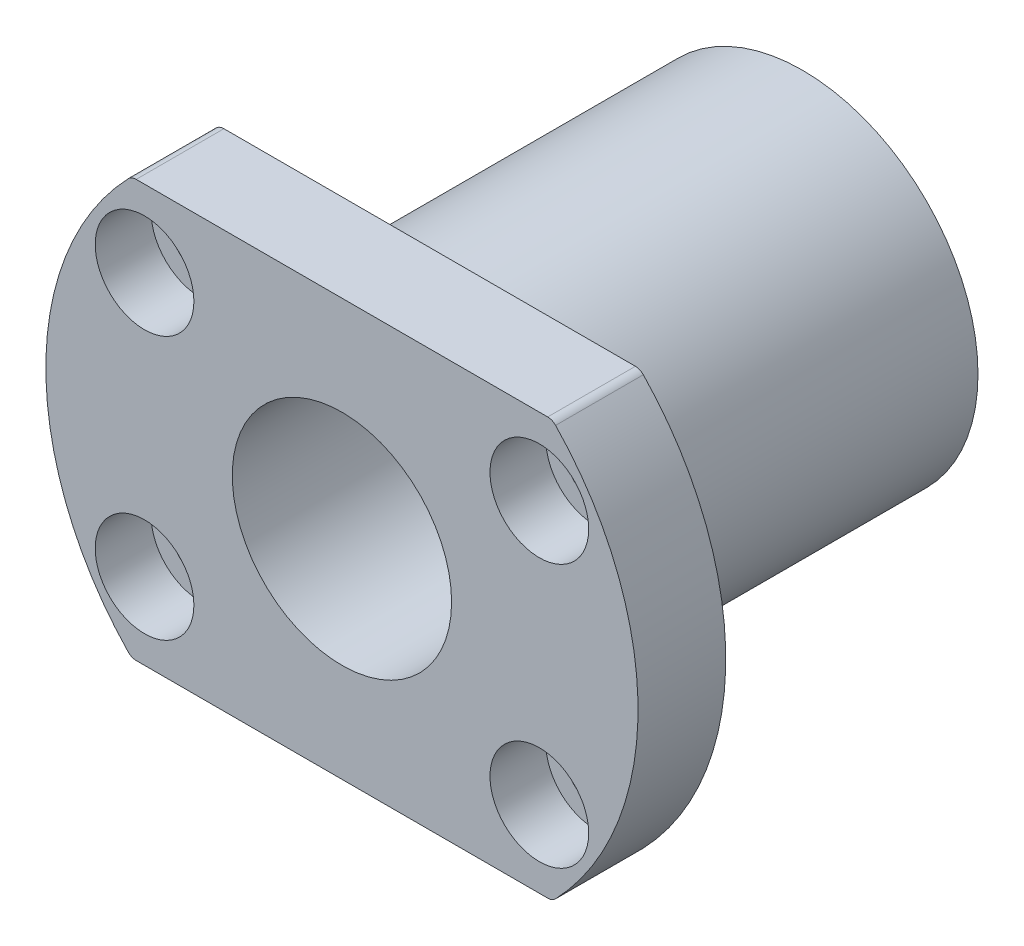
SolidWorks part; units mm, degrees
ref_plane "Front Plane" through (0, 0, 0) normal (0, 0, 1) x (1, 0, 0)
ref_plane "Top Plane" through (0, 0, 0) normal (0, 1, 0) x (1, 0, 0)
ref_plane "Right Plane" through (0, 0, 0) normal (1, 0, 0) x (0, 0, -1)
sketch "Sketch1" plane through (0, 0, 0) normal (0, 0, 1) x (1, 0, 0)
  circle A0 centre (0, 0) radius 16
  circle A1 centre (0, 0) radius 10
  dimension "D1" = 20
  dimension "D2" = 32
extrude "Boss-Extrude1" add sketch "Sketch1" along normal blind 34
sketch "Sketch2" plane through (0, 0, 34) normal (0, 0, 1) x (1, 0, 0)
  line L0 (0, 0) -> (31.8215, 0) construction
  line L1 (-19.1833, -19) -> (19.1833, -19)
  line L2 (-19.1833, 19) -> (19.1833, 19)
  arc A0 (19.1833, -19) -> (19.1833, 19) centre (0, 0) ccw
  arc A1 (-19.1833, 19) -> (-19.1833, -19) centre (0, 0) ccw
  circle A2 centre (0, 0) radius 10 construction
  circle A3 centre (0, 0) radius 10
  dimension "D1" = 54
  dimension "D2" = 19
extrude "Boss-Extrude2" add sketch "Sketch2" along normal blind 8
sketch "Sketch3" plane through (0, 0, 42) normal (0, 0, 1) x (1, 0, 0)
  line L0 (0, 0) -> (0, 22.5899) construction
  line L1 (0, 0) -> (-30.772, 0) construction
  circle A0 centre (-18, 12) radius 3.5851
  circle A1 centre (-18, -12) radius 3.5851
  circle A2 centre (18, 12) radius 3.5851
  circle A3 centre (18, -12) radius 3.5851
  dimension "D1" = 18
  dimension "D2" = 12
hole_wizard "CBORE for M5 Hex Socket Head Cap Screw1" positions "3DSketch1" profile "Sketch4" counterbore size "M5" standard "ISO" end condition through all
sketch3d "3DSketch1"
  point P0 (-18, -12, 42)
  point P3 (-18, 12, 42)
  point P6 (18, 12, 42)
  point P9 (18, -12, 42)
sketch "Sketch4" plane through (-18, -12, 42) normal (1, 0, 0) x (0, -1, 0)
  line L0 (0, 0) -> (0, 42)
  line L1 (0, 42) -> (2.75, 42)
  line L3 (2.75, 42) -> (2.75, 5.1)
  line L4 (2.75, 5.1) -> (4.5, 5.1)
  line L5 (4.5, 5.1) -> (4.5, 0)
  line L7 (4.5, 0) -> (0, 0)
  line L11 (0, -6.35) -> (0, 107.95) construction
  dimension "Thru Hole Dia." = 5.5
  dimension "Thru Hole Depth" = 42
  dimension "C'Bore Dia." = 9
  dimension "C'Bore Depth" = 5.1
fillet "Fillet1" radius 1 4 edges at (19.1833, 19, 38) (-19.1833, 19, 38) (-19.1833, -19, 38) (19.1833, -19, 38)
